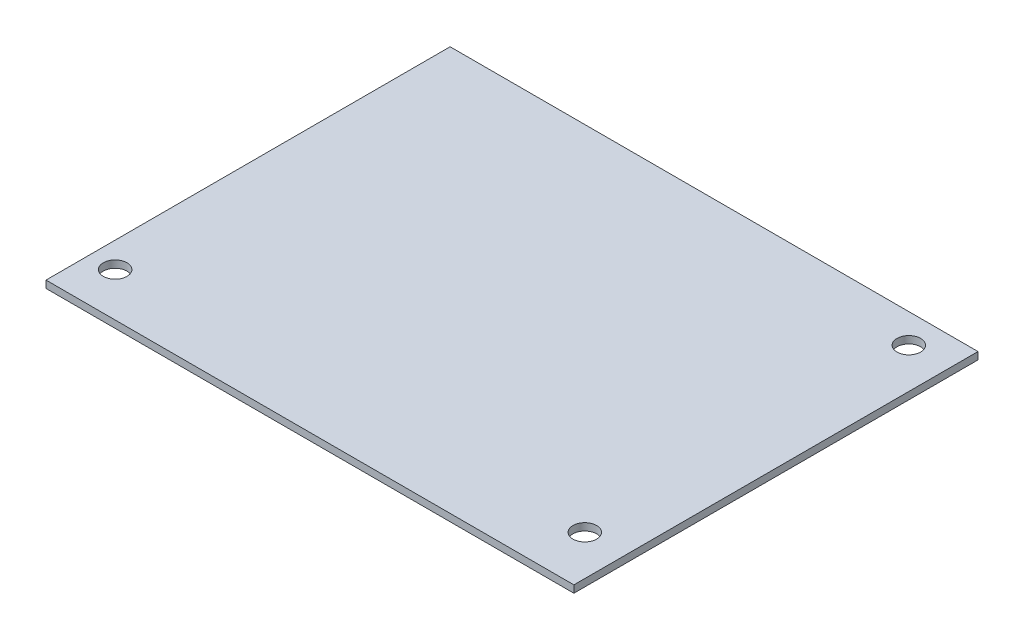
SolidWorks part; units mm, degrees
ref_plane "Front Plane" through (0, 0, 0) normal (0, 0, 1) x (1, 0, 0)
ref_plane "Top Plane" through (0, 0, 0) normal (0, 1, 0) x (1, 0, 0)
ref_plane "Right Plane" through (0, 0, 0) normal (1, 0, 0) x (0, 0, -1)
sketch "Sketch1" plane through (0, 0, 0) normal (0, 1, 0) x (1, 0, 0)
  line L1 (0, 0) -> (-145, 0)
  line L2 (0, 0) -> (0, 111)
  line L3 (0, 111) -> (-145, 111)
  line L4 (-145, 0) -> (-145, 111)
  circle A0 centre (-138, 12) radius 3.25
  circle A1 centre (-11, 14) radius 3.25
  circle A2 centre (-11, 103) radius 3.25
  dimension "D3" = 6.5
  dimension "D6" = 6.5
  dimension "D7" = 11
  dimension "D8" = 14
  dimension "D9" = 6.5
  dimension "D10" = 11
  dimension "D11" = 8
  dimension "D1" = 145
  dimension "D2" = 111
  dimension "D4" = 7
  dimension "D5" = 12
extrude "Boss-Extrude1" add sketch "Sketch1" along normal blind 2
